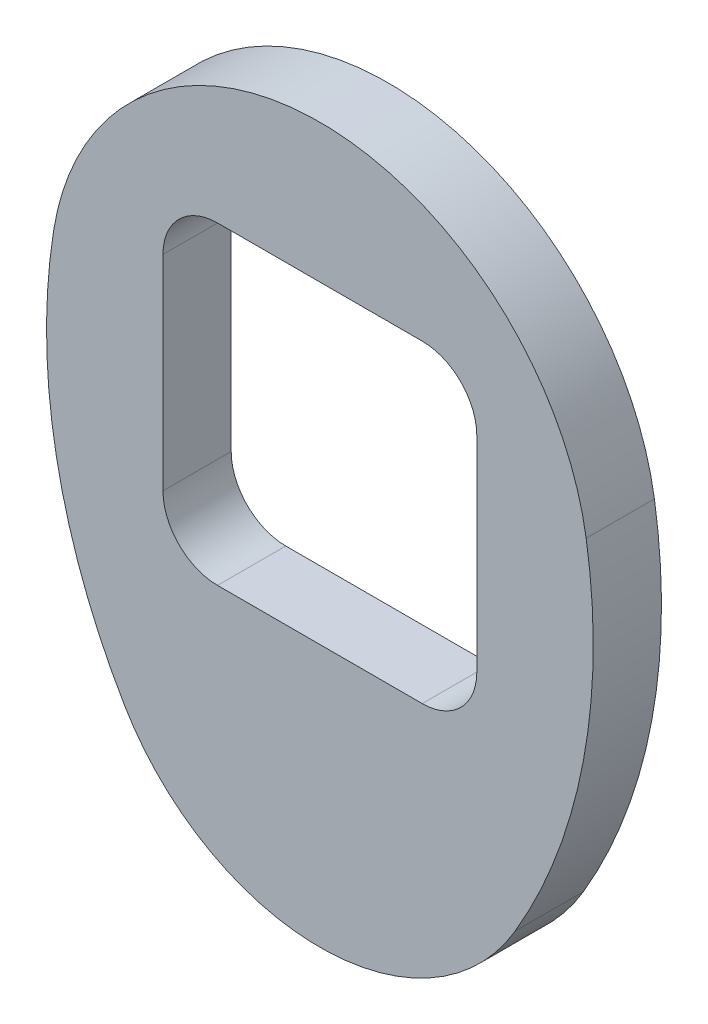
SolidWorks part; units mm, degrees
material "Balsa"
ref_plane "Front Plane" through (0, 0, 0) normal (0, 0, 1) x (1, 0, 0)
ref_plane "Top Plane" through (0, 0, 0) normal (0, 1, 0) x (1, 0, 0)
ref_plane "Right Plane" through (0, 0, 0) normal (1, 0, 0) x (0, 0, -1)
sketch "Sketch1" plane through (0, 0, 0) normal (0, 0, 1) x (1, 0, 0)
  line L8 (-12.7, 0) -> (12.7, 0) construction
  line L9 (-24.784, 31.75) -> (24.784, 31.75)
  line L10 (-19.05, 25.4) -> (19.05, 25.4)
  line L14 (-18.9836, 20.32) -> (18.9836, 20.32)
  line L21 (-18.173, -3.2201) -> (-12.7, 0)
  line L22 (12.7, 0) -> (18.173, -3.2201)
  arc A0 (19.05, 25.4) -> (12.7, 0) centre (-27.18, 23.4638) cw
  arc A1 (-19.05, 25.4) -> (-12.7, 0) centre (27.18, 23.4638) ccw
  arc A2 (-24.784, 31.75) -> (-18.173, -3.2201) centre (27.18, 23.4638) ccw
  arc A3 (24.784, 31.75) -> (18.173, -3.2201) centre (-27.18, 23.4638) cw
  arc A4 (-25.3944, 25.6657) -> (-18.173, -3.2201) centre (27.18, 23.4638) ccw construction
  arc A5 (25.3944, 25.6657) -> (18.173, -3.2201) centre (-27.18, 23.4638) cw construction
  arc A6 (19.05, 25.4) -> (12.7, 0) centre (-27.18, 23.4638) cw construction
  arc A7 (-19.05, 25.4) -> (-12.7, 0) centre (27.18, 23.4638) ccw construction
  arc A8 (-24.784, 31.75) -> (24.784, 31.75) centre (0, 27.7979) cw
  arc A9 (-12.7, 0) -> (12.7, 0) centre (0, 7.4722) ccw
  arc A10 (-18.173, -3.2201) -> (18.173, -3.2201) centre (0, 7.4722) ccw
  point P0 (0, 0)
  point P13 (0, 25.4)
  dimension "D7" = 25.4
  dimension "D2" = 46.2705
  dimension "D8" = 5.08
  dimension "D3" = 25.4
  dimension "D6" = 38.1
  dimension "D1" = 6.35
  dimension "D4" = 6.35
  dimension "D5" = 6.35
extrude "Boss-Extrude1" add sketch "Sketch1" along normal blind 6.35
sketch "Sketch2" plane through (0, 0, 6.35) normal (0, 0, 1) x (1, 0, 0)
  line L0 (0, 0) -> (0, 52.895) construction
  line L1 (-14.605, 40.005) -> (14.605, 40.005)
  line L2 (-14.605, 40.005) -> (-14.605, 10.795)
  line L3 (-14.605, 10.795) -> (14.605, 10.795)
  line L4 (14.605, 40.005) -> (14.605, 10.795)
  line L5 (-14.605, 40.005) -> (14.605, 10.795) construction
  line L6 (-14.605, 10.795) -> (14.605, 40.005) construction
  arc A0 (24.784, 31.75) -> (-24.784, 31.75) centre (0, 27.7979) ccw construction
  point P0 (0, 25.4)
  dimension "D1" = 29.21
  dimension "D2" = 29.21
  dimension "D3" = 25.4
extrude "Cut-Extrude1" cut sketch "Sketch2" against normal up to next
fillet "Fillet1" radius 5.08 4 edges at (14.605, 10.795, 3.175) (14.605, 40.005, 3.175) (-14.605, 40.005, 3.175) (-14.605, 10.795, 3.175)
